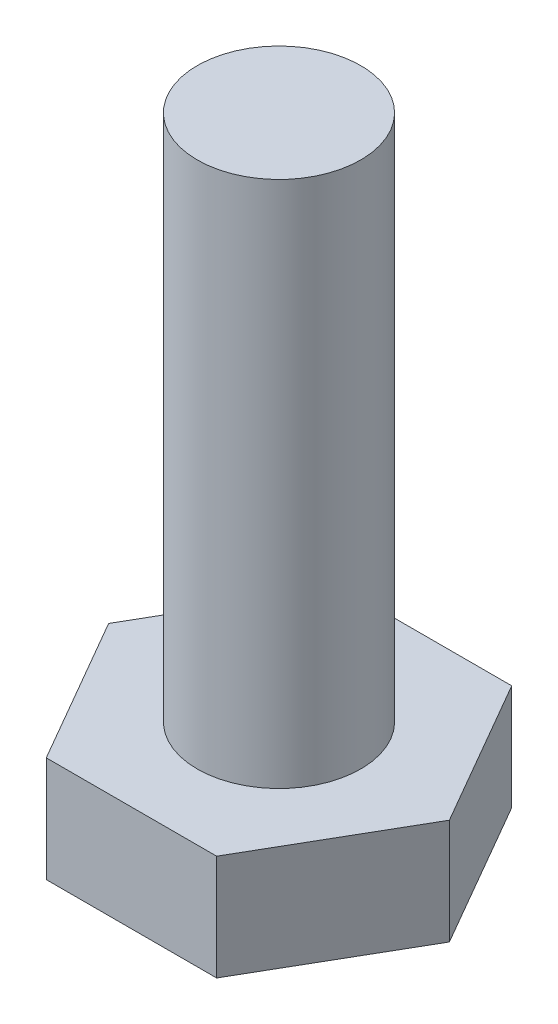
SolidWorks part; units mm, degrees
ref_plane "정면" through (0, 0, 0) normal (0, 0, 1) x (1, 0, 0)
ref_plane "윗면" through (0, 0, 0) normal (0, 1, 0) x (1, 0, 0)
ref_plane "우측면" through (0, 0, 0) normal (1, 0, 0) x (0, 0, -1)
sketch "스케치1" plane through (0, 0, 0) normal (0, 1, 0) x (1, 0, 0)
  line L1 (3.23, 0) -> (1.615, 2.7973)
  line L2 (1.615, 2.7973) -> (-1.615, 2.7973)
  line L3 (-1.615, 2.7973) -> (-3.23, 0)
  line L4 (-3.23, 0) -> (-1.615, -2.7973)
  line L5 (-1.615, -2.7973) -> (1.615, -2.7973)
  line L6 (1.615, -2.7973) -> (3.23, 0)
  circle A0 centre (0, 0) radius 2.7973 construction
  dimension "D1" = 3.23
extrude "보스-돌출1" add sketch "스케치1" along normal blind 2
sketch "스케치2" plane through (0, 2, 0) normal (0, 1, 0) x (1, 0, 0)
  circle A0 centre (0, 0) radius 1.55
  dimension "D1" = 3.1
extrude "보스-돌출2" add sketch "스케치2" along normal blind 10
